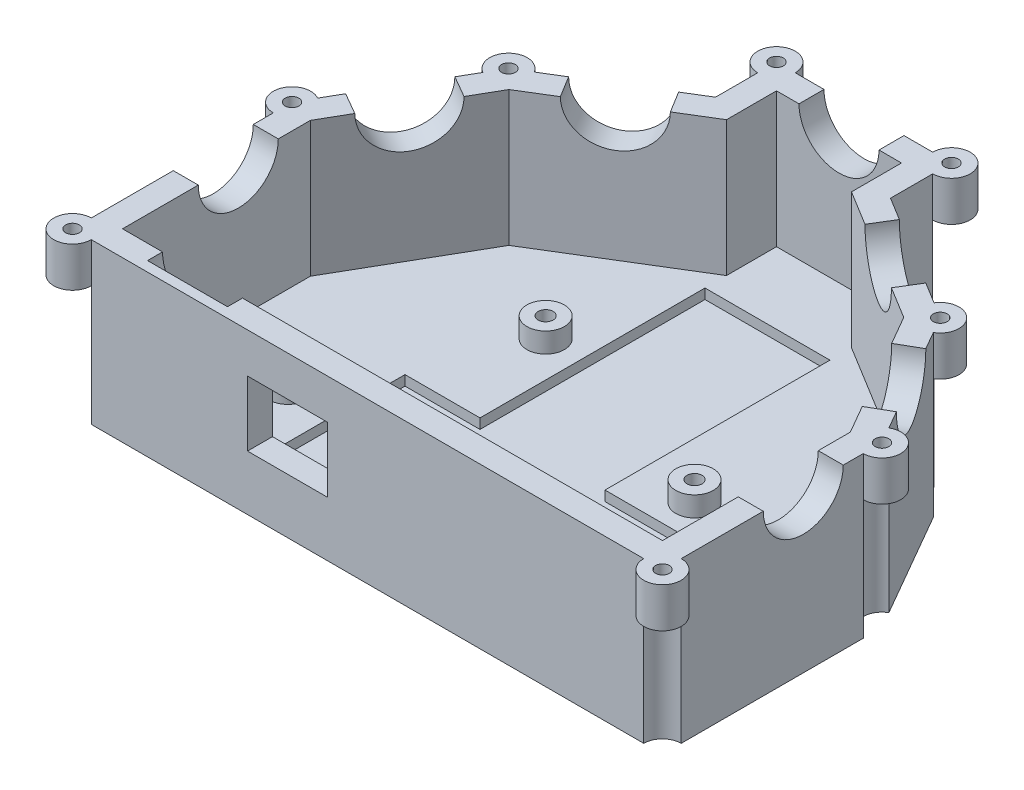
SolidWorks part; units mm, degrees
ref_plane "Front Plane" through (0, 0, 0) normal (0, 0, 1) x (1, 0, 0)
ref_plane "Top Plane" through (0, 0, 0) normal (0, 1, 0) x (1, 0, 0)
ref_plane "Right Plane" through (0, 0, 0) normal (1, 0, 0) x (0, 0, -1)
sketch "Sketch1" plane through (0, 0, 0) normal (0, 1, 0) x (1, 0, 0)
  line L0 (-50, -32.5) -> (50, -32.5)
  line L1 (50, -32.5) -> (50, 0)
  line L2 (50, 0) -> (36.5236, 23.3963)
  line L3 (36.5236, 23.3963) -> (13.5, 37.5)
  line L4 (13.5, 37.5) -> (-13.5, 37.5)
  line L5 (-13.5, 37.5) -> (-36.5236, 23.3963)
  line L6 (-36.5236, 23.3963) -> (-50, 0)
  line L7 (-50, 0) -> (-50, -32.5)
  line L8 (-43.1787, 29.8739) -> (-17.5, 45.6041)
  line L10 (17.5, 45.6041) -> (43.1787, 29.8739)
  line L11 (43.1787, 29.8739) -> (59, 2.4067)
  line L12 (-43.1787, 29.8739) -> (-59, 2.4067)
  line L13 (-59, 2.4067) -> (-59, -41.5)
  line L14 (-59, -41.5) -> (59, -41.5)
  line L15 (59, -41.5) -> (59, 2.4067)
  line L16 (-50, 0) -> (50, 0) construction
  line L17 (-13.5, 37.5) -> (0, 0) construction
  line L18 (0, 0) -> (13.5, 37.5) construction
  line L19 (0, 0) -> (36.5236, 23.3963) construction
  line L20 (-36.5236, 23.3963) -> (0, 0) construction
  line L21 (39.4814, 26.2752) -> (12.5, 42.8034)
  line L23 (-12.5, 42.8034) -> (-39.4814, 26.2752)
  line L24 (-39.4814, 26.2752) -> (-54, 1.0696)
  line L25 (-54, 1.0696) -> (-54, -36.5)
  line L26 (-54, -36.5) -> (54, -36.5)
  line L27 (54, -36.5) -> (54, 1.0696)
  line L28 (54, 1.0696) -> (39.4814, 26.2752)
  line L29 (17.5, 45.6041) -> (17.5, 57.8034)
  line L30 (17.5, 57.8034) -> (-17.5, 57.8034)
  line L31 (-17.5, 57.8034) -> (-17.5, 45.6041)
  line L32 (12.5, 42.8034) -> (12.5, 52.8034)
  line L33 (12.5, 52.8034) -> (-12.5, 52.8034)
  line L34 (-12.5, 52.8034) -> (-12.5, 42.8034)
  dimension "D4" = 10
  dimension "D1" = 100
  dimension "D2" = 70
  dimension "D3" = 27
  dimension "D5" = 27
  dimension "D7" = 27
  dimension "D8" = 32.5
  dimension "D16" = 5
  dimension "D17" = 9
  dimension "D18" = 9
  dimension "D19" = 9
  dimension "D20" = 9
  dimension "D21" = 9
  dimension "D22" = 9
  dimension "D23" = 9
  dimension "D24" = 5
  dimension "D25" = 5
  dimension "D26" = 5
  dimension "D27" = 5
  dimension "D28" = 5
  dimension "D29" = 5
  dimension "D30" = 5
  dimension "D31" = 5
  dimension "D32" = 5
  dimension "D33" = 25
extrude "Boss-Extrude2" add sketch "Sketch1" along normal blind 27 contours L8 L31 L30 L29 L10 L11 L15 L14 L13 L12 | L34 L23 L24 L25 L26 L27 L28 L21 L32 L33
sketch "Sketch2" plane through (0, 0, 0) normal (0, -1, 0) x (1, 0, 0)
  line L0 (17.5, -57.8034) -> (-17.5, -57.8034)
  line L1 (-17.5, -57.8034) -> (-17.5, -45.6041)
  line L2 (-17.5, -45.6041) -> (-43.1787, -29.8739)
  line L3 (-43.1787, -29.8739) -> (-59, -2.4067)
  line L4 (-59, -2.4067) -> (-59, 41.5)
  line L5 (-59, 41.5) -> (59, 41.5)
  line L6 (59, 41.5) -> (59, -2.4067)
  line L7 (59, -2.4067) -> (43.1787, -29.8739)
  line L8 (43.1787, -29.8739) -> (17.5, -45.6041)
  line L9 (17.5, -45.6041) -> (17.5, -57.8034)
extrude "Boss-Extrude3" add sketch "Sketch2" along normal blind 5
sketch "Sketch3" plane through (0, -5, 0) normal (0, -1, 0) x (-1, 0, 0)
  line L0 (-59, -41.5) -> (59, -41.5) construction
  line L1 (-59, 2.4067) -> (-59, -41.5) construction
  line L2 (59, -41.5) -> (59, 2.4067) construction
  circle A0 centre (-45.36, -27.86) radius 1.5
  circle A1 centre (-23.64, 0.27) radius 1.5
  circle A2 centre (19.63, 13.76) radius 1.5
  circle A3 centre (36.69, -20.73) radius 1.5
  dimension "D1" = 3
  dimension "D2" = 13.64
  dimension "D3" = 13.64
  dimension "D4" = 41.77
  dimension "D5" = 35.36
  dimension "D6" = 39.37
  dimension "D7" = 55.26
  dimension "D8" = 20.77
  dimension "D9" = 22.31
sketch "Sketch6" plane through (0, 0, 0) normal (0, 1, 0) x (1, 0, 0)
  circle A0 centre (-19.63, 13.76) radius 3.75
  circle A1 centre (-36.69, -20.73) radius 3.75
  circle A2 centre (23.64, 0.27) radius 3.75
  circle A3 centre (45.36, -27.86) radius 3.75
  dimension "D1" = 7.5
extrude "Boss-Extrude8" add sketch "Sketch6" along normal blind 4
extrude "Cut-Extrude2" cut sketch "Sketch3" against normal through all
sketch "Sketch7" plane through (0, 27, 0) normal (0, 1, 0) x (1, 0, 0)
  circle A0 centre (-59, -41.5) radius 3.75
  circle A1 centre (-59, 2.4067) radius 3.75
  circle A2 centre (-43.1787, 29.8739) radius 3.75
  circle A4 centre (-17.5, 57.8034) radius 3.75
  circle A5 centre (17.5, 57.8034) radius 3.75
  circle A7 centre (43.1787, 29.8739) radius 3.75
  circle A8 centre (59, 2.4067) radius 3.75
  circle A9 centre (59, -41.5) radius 3.75
  dimension "D1" = 7.5
extrude "Boss-Extrude9" add sketch "Sketch7" against normal blind 8
sketch "Sketch8" plane through (0, -5, 0) normal (0, -1, 0) x (1, 0, 0)
  circle A0 centre (59, 41.5) radius 3.75
  circle A1 centre (59, -2.4067) radius 3.75
  circle A2 centre (43.1787, -29.8739) radius 3.75
  circle A4 centre (17.5, -57.8034) radius 3.75
  circle A5 centre (-17.5, -57.8034) radius 3.75
  circle A7 centre (-43.1787, -29.8739) radius 3.75
  circle A8 centre (-59, -2.4067) radius 3.75
  circle A9 centre (-59, 41.5) radius 3.75
  dimension "D1" = 7.5
extrude "Cut-Extrude4" cut sketch "Sketch8" against normal up to surface (24 mm away) up to face at (59.2589, 19, 41.7589)
sketch "Sketch9" plane through (0, 27, 0) normal (0, 1, 0) x (1, 0, 0)
  circle A0 centre (-59, -41.5) radius 1.375
  circle A1 centre (-59, 2.4067) radius 1.375
  circle A2 centre (-17.5, 57.8034) radius 1.375
  circle A4 centre (43.1787, 29.8739) radius 1.375
  circle A6 centre (17.5, 57.8034) radius 1.375
  circle A7 centre (-43.1787, 29.8739) radius 1.375
  circle A8 centre (59, 2.4067) radius 1.375
  circle A9 centre (59, -41.5) radius 1.375
  dimension "D1" = 2.75
extrude "Cut-Extrude5" cut sketch "Sketch9" against normal through all
sketch "Sketch11" plane through (0, 0, 0) normal (0, 1, 0) x (1, 0, 0)
  line L0 (0, 0) -> (12.5, 38.5) construction
  line L1 (-54, -36.5) -> (54, -36.5) construction
  line L2 (27.5, -36.5) -> (27.5, -6.5)
  line L3 (27.5, -6.5) -> (12.5, -6.5)
  line L4 (12.5, -6.5) -> (12.5, 38.5)
  line L5 (12.5, 38.5) -> (-12.5, 38.5)
  line L6 (-12.5, 38.5) -> (-12.5, -6.5)
  line L7 (-12.5, -6.5) -> (-27.5, -6.5)
  line L8 (-27.5, -6.5) -> (-27.5, -36.5)
  line L9 (-54, -36.5) -> (54, -36.5) construction
  line L10 (-27.5, -36.5) -> (27.5, -36.5)
  line L11 (-12.5, 38.5) -> (0, 0) construction
  dimension "D1" = 15
  dimension "D2" = 25
  dimension "D3" = 45
  dimension "D4" = 30
extrude "Cut-Extrude6" cut sketch "Sketch11" against normal blind 2
sketch "Sketch13" plane through (-59, 0, 0) normal (-1, 0, 0) x (0, 0, 1)
  line L0 (1.3433, 27) -> (37.75, 27) construction
  line L1 (1.3433, 19) -> (1.3433, -5) construction
  circle A0 centre (13.3433, 27) radius 8
  dimension "D1" = 16
  dimension "D2" = 12
extrude "Cut-Extrude8" cut sketch "Sketch13" against normal through all
sketch "Sketch14" plane through (-45.3424, 0, -26.1175) normal (-0.8665, 0, -0.4991) x (-0.4991, 0, 0.8665)
  line L0 (-0.585, 27) -> (23.613, 27) construction
  circle A0 centre (11.514, 27) radius 8
  dimension "D1" = 16
extrude "Cut-Extrude9" cut sketch "Sketch14" against normal up to next
sketch "Sketch16" plane through (0, 0, -57.8034) normal (0, 0, -1) x (-1, 0, 0)
  line L0 (-13.75, 27) -> (13.75, 27) construction
  circle A0 centre (0, 27) radius 8
  dimension "D1" = 16
extrude "Cut-Extrude11" cut sketch "Sketch16" against normal up to next
sketch "Sketch17" plane through (45.3424, 0, -26.1175) normal (0.8665, 0, -0.4991) x (-0.4991, 0, -0.8665)
  line L0 (0.585, 27) -> (-23.613, 27) construction
  circle A0 centre (-11.514, 27) radius 8
  dimension "D1" = 16
extrude "Cut-Extrude12" cut sketch "Sketch17" against normal up to next
sketch "Sketch19" plane through (-25.0884, 0, -40.9556) normal (-0.5224, 0, -0.8527) x (-0.8527, 0, 0.5224)
  line L0 (17.4646, 27) -> (-8.8991, 27) construction
  line L1 (17.4646, 27) -> (17.4646, 19) construction
  circle A0 centre (4.4646, 27) radius 8
  dimension "D1" = 16
  dimension "D2" = 13
extrude "Cut-Extrude13" cut sketch "Sketch19" against normal up to next
sketch "Sketch20" plane through (25.0884, 0, -40.9556) normal (0.5224, 0, -0.8527) x (-0.8527, 0, -0.5224)
  line L0 (8.8991, 27) -> (-17.4646, 27) construction
  line L1 (-17.4646, 19) -> (-17.4646, 27) construction
  circle A0 centre (-4.4646, 27) radius 8
  dimension "D1" = 16
  dimension "D2" = 13
extrude "Cut-Extrude14" cut sketch "Sketch20" against normal up to next
sketch "Sketch21" plane through (0, 0, 36.5) normal (0, 0, -1) x (-1, 0, 0)
  line L0 (54, 27) -> (-54, 27) construction
  line L1 (-32, 19) -> (-16, 19)
  line L2 (-32, 19) -> (-32, 6)
  line L3 (-32, 6) -> (-16, 6)
  line L4 (-16, 19) -> (-16, 6)
  line L5 (54, 27) -> (54, 0) construction
  line L6 (-54, 27) -> (-54, 0) construction
  circle A0 centre (38, 27) radius 8
  dimension "D1" = 16
  dimension "D2" = 16
  dimension "D3" = 16
  dimension "D4" = 13
  dimension "D5" = 22
  dimension "D6" = 8
extrude "Cut-Extrude15" cut sketch "Sketch21" against normal blind 3
sketch "Sketch22" plane through (0, 0, 36.5) normal (0, 0, -1) x (-1, 0, 0)
  line L0 (30, 27) -> (-54, 27) construction
  line L1 (8, 6) -> (24, 6)
  line L2 (8, 6) -> (8, 19)
  line L3 (8, 19) -> (24, 19)
  line L4 (24, 6) -> (24, 19)
  line L6 (-16, 6) -> (-16, 19) construction
  dimension "D1" = 16
  dimension "D2" = 13
  dimension "D3" = 8
  dimension "D4" = 24
extrude "Cut-Extrude16" cut sketch "Sketch22" against normal through all
